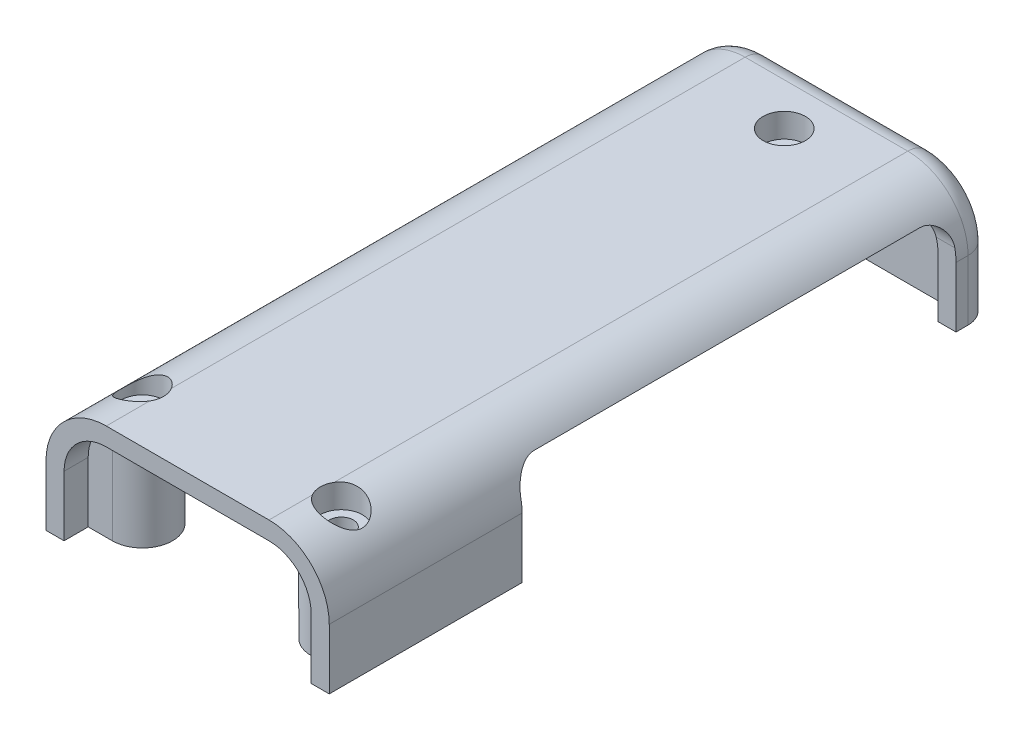
SolidWorks part; units mm, degrees
ref_plane "Front Plane" through (0, 0, 0) normal (0, 0, 1) x (1, 0, 0)
ref_plane "Top Plane" through (0, 0, 0) normal (0, 1, 0) x (1, 0, 0)
ref_plane "Right Plane" through (0, 0, 0) normal (1, 0, 0) x (0, 0, -1)
sketch "Sketch1" plane through (0, 0, 0) normal (0, 0, 1) x (1, 0, 0)
  line L0 (0, -24.4696) -> (0, 33.8552) construction
  line L1 (-46.7604, 0) -> (49.2743, 0) construction
  line L2 (10.25, 0) -> (10.25, 5)
  line L3 (11.75, 0) -> (11.75, 5)
  line L4 (-6.75, 8.5) -> (6.75, 8.5)
  line L5 (-6.75, 10) -> (6.75, 10)
  line L6 (9.0437, 5) -> (22.7817, 5) construction
  line L7 (6.75, 8.0974) -> (6.75, 12.4299) construction
  line L8 (10.25, 0) -> (11.75, 0)
  line L9 (-11.75, 0) -> (-11.75, 5)
  line L10 (-10.25, 0) -> (-11.75, 0)
  line L11 (-10.25, 0) -> (-10.25, 5)
  arc A0 (6.75, 8.5) -> (10.25, 5) centre (6.75, 5) cw
  arc A1 (6.75, 10) -> (11.75, 5) centre (6.75, 5) cw
  arc A2 (-6.75, 10) -> (-11.75, 5) centre (-6.75, 5) ccw
  arc A3 (-6.75, 8.5) -> (-10.25, 5) centre (-6.75, 5) ccw
  point P20 (0, 10)
  point P26 (0, 8.5)
  dimension "D4" = 5
  dimension "D1" = 11.75
  dimension "D2" = 1.5
  dimension "D3" = 10
extrude "Boss-Extrude1" add sketch "Sketch1" along normal blind 53.5
sketch "Sketch2" plane through (0, 0, 0) normal (0, 0, 1) x (1, 0, 0)
  line L0 (-11.75, 0) -> (11.75, 0)
  line L1 (11.75, 0) -> (11.75, 5)
  line L2 (6.75, 10) -> (-6.75, 10)
  line L3 (-11.75, 0) -> (-11.75, 5)
  arc A0 (-11.75, 5) -> (-6.75, 10) centre (-6.75, 5) cw
  arc A1 (11.75, 5) -> (6.75, 10) centre (6.75, 5) ccw
extrude "Boss-Extrude2" add sketch "Sketch2" against normal blind 1.5
sketch "Sketch3" plane through (11.75, 0, 0) normal (1, 0, 0) x (0, 0, -1)
  line L0 (-19.5, -2.8502) -> (-19.5, 11.6128) construction
  line L1 (-8, 0) -> (-1.5, 0)
  line L2 (-53.5, 0) -> (1.5, 0) construction
  line L3 (-1.5, 0) -> (-1.5, 6)
  line L4 (-35.5, 8) -> (-3.5, 8)
  line L5 (-37.5, 0) -> (-37.5, 6)
  line L6 (-8, 0) -> (-37.5, 0)
  arc A0 (-1.5, 6) -> (-3.5, 8) centre (-3.5, 6) ccw
  arc A1 (-37.5, 6) -> (-35.5, 8) centre (-35.5, 6) cw
  point P14 (-19.5, 8)
  dimension "D1" = 2
  dimension "D2" = 8
  dimension "D3" = 18
  dimension "D4" = 19.5
extrude "Cut-Extrude1" cut sketch "Sketch3" against normal blind 3
sketch "Sketch4" plane through (0, 0, 0) normal (0, -1, 0) x (1, 0, 0)
  line L0 (0, -5.1254) -> (0, 35.2905) construction
  line L1 (2.5, 0) -> (2.5, 4)
  line L2 (-10.25, 0) -> (10.25, 0) construction
  line L3 (-2.5, 0) -> (-2.5, 4)
  line L4 (-18.3062, 49) -> (17.3088, 49) construction
  line L5 (10.25, 51.5) -> (8.25, 51.5)
  line L6 (10.25, 53.5) -> (10.25, 37.5) construction
  line L7 (10.25, 51.5) -> (10.25, 46.5)
  line L8 (2.5, 0) -> (-2.5, 0)
  line L9 (10.25, 53.5) -> (10.25, 37.5) construction
  line L10 (10.25, 46.5) -> (8.25, 46.5)
  line L11 (-10.25, 51.5) -> (-10.25, 46.5)
  line L12 (-10.25, 46.5) -> (-8.25, 46.5)
  line L13 (-10.25, 51.5) -> (-8.25, 51.5)
  arc A0 (2.5, 4) -> (-2.5, 4) centre (0, 4) ccw
  arc A2 (8.25, 51.5) -> (8.25, 46.5) centre (8.25, 49) ccw
  arc A3 (-8.25, 51.5) -> (-8.25, 46.5) centre (-8.25, 49) cw
  point P11 (10.25, 49)
  point P19 (0, 0)
  dimension "D2" = 2.5
  dimension "D3" = 45
  dimension "D4" = 2.5
  dimension "D1" = 4
  dimension "D5" = 2
extrude "Boss-Extrude3" add sketch "Sketch4" against normal up to surface (8.5 mm away) up to face at (0, 8.5, 26.75)
sketch "Sketch5" plane through (0, 0, 0) normal (0, -1, 0) x (1, 0, 0)
  circle A0 centre (0, 4) radius 1
  circle A1 centre (8.25, 49) radius 1
  circle A2 centre (-8.25, 49) radius 1
  dimension "D1" = 2
extrude "Cut-Extrude2" cut sketch "Sketch5" against normal up to surface (10 mm away) up to face at (0, 10, 26)
sketch "Sketch6" plane through (0, 10, 0) normal (0, 1, 0) x (1, 0, 0)
  point P0 (0, -4)
  point P1 (-8.25, -49)
  point P3 (8.25, -49)
hole_wizard "Hole1" positions "Sketch7" profile "Sketch8" legacy end condition through all
sketch "Sketch7" plane through (0, 10, 0) normal (0, 1, 0) x (1, 0, 0)
  point P0 (0, -4)
  point P3 (-8.25, -49)
  point P6 (8.25, -49)
sketch "Sketch8" plane through (0, 10, 4) normal (1, 0, 0) x (0, 0, 1)
  line L0 (0, 0) -> (0, 10)
  line L1 (0, 10) -> (1, 10)
  line L2 (1, 10) -> (1, 2)
  line L3 (1, 2) -> (1.75, 2)
  line L4 (1.75, 2) -> (1.75, 0)
  line L5 (1.75, 0) -> (0, 0)
  line L6 (0, 110) -> (0, -10) construction
  dimension "Diameter" = 2
  dimension "Depth" = 10
  dimension "C-Bore Diameter" = 3.5
  dimension "C-Bore Depth" = 2
sketch "Sketch10" plane through (-11.75, 0, 0) normal (-1, 0, 0) x (0, 0, 1)
  line L0 (8, -3.4314) -> (8, 15.5314) construction
  line L1 (4, 0) -> (4, 4)
  line L2 (53.5, 0) -> (-1.5, 0) construction
  line L3 (10, 6) -> (6, 6)
  line L4 (4, 0) -> (12, 0)
  line L5 (12, 0) -> (12, 4)
  line L6 (0, -3.2088) -> (0, 12.5587) construction
  arc A0 (4, 4) -> (6, 6) centre (6, 4) cw
  arc A1 (12, 4) -> (10, 6) centre (10, 4) ccw
  point P11 (8, 6)
  point P14 (8, 0)
  dimension "D2" = 2
  dimension "D1" = 4
  dimension "D3" = 6
  dimension "D4" = 8
extrude "Cut-Extrude4" cut sketch "Sketch10" against normal blind 3
fillet "Fillet1" radius 2 5 edges at (11.75, 2.5, -1.5) (10.2855, 8.5355, -1.5) (-11.75, 2.5, -1.5) (-10.2855, 8.5355, -1.5) (0, 10, -1.5)
